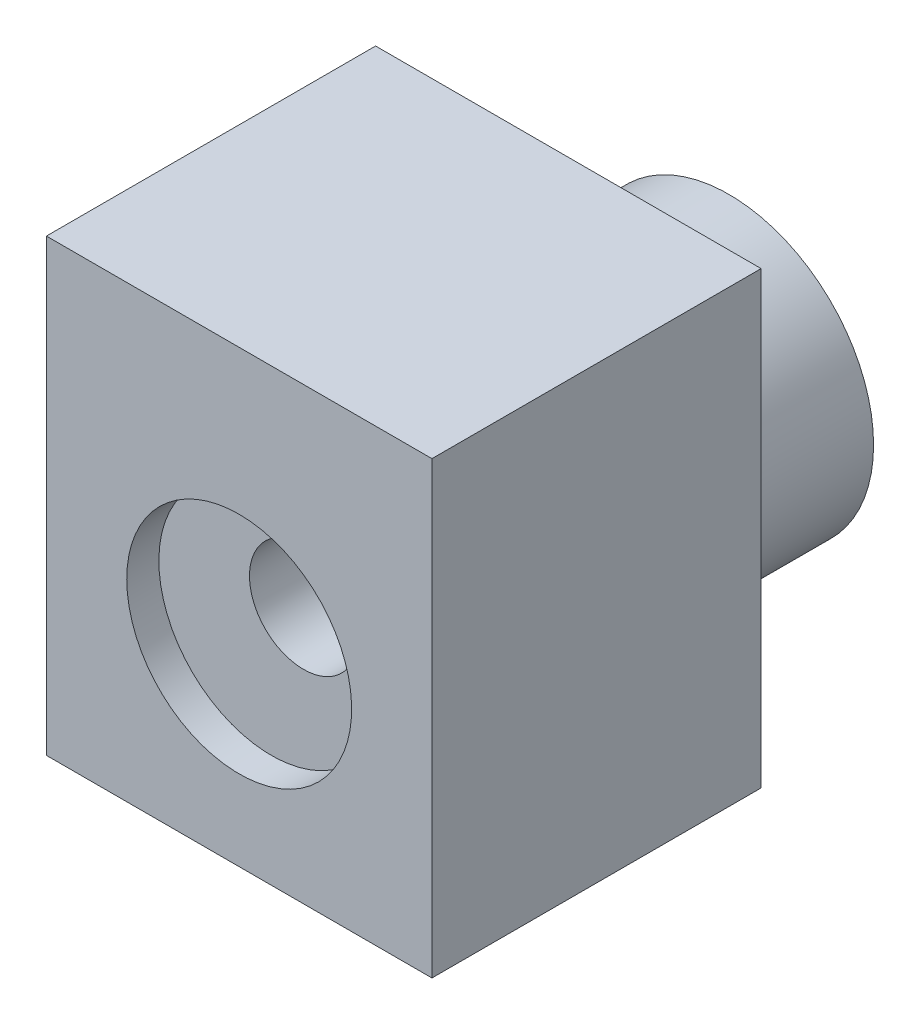
SolidWorks part; units mm, degrees
ref_plane "Płaszczyzna przednia" through (0, 0, 0) normal (0, 0, 1) x (1, 0, 0)
ref_plane "Płaszczyzna górna" through (0, 0, 0) normal (0, 1, 0) x (1, 0, 0)
ref_plane "Płaszczyzna prawa" through (0, 0, 0) normal (1, 0, 0) x (0, 0, -1)
sketch "Szkic2" plane through (0, 0, 0) normal (0, 1, 0) x (1, 0, 0)
  line L0 (13.5, 19) -> (9.3722, 19) construction
  line L1 (-30, 14) -> (30, 14)
  line L2 (-30, 14) -> (-30, 65.2287)
  line L3 (-30, 65.2287) -> (30, 65.2287)
  line L4 (30, 14) -> (30, 65.2287)
  line L5 (-30, 14) -> (30, 65.2287) construction
  line L6 (-30, 65.2287) -> (30, 14) construction
  line L7 (-12, 60.2287) -> (12, 60.2287) construction
  line L8 (0, 0) -> (0, 144.3077) construction
  point P0 (0, 39.6144)
  point P12 (0, 0)
  dimension "D1" = 5
  dimension "D2" = 5
  dimension "D3" = 60
extrude "Dodanie-wyciągnięcie1" add sketch "Szkic2" against normal blind 30 and the other way blind 40
sketch "Szkic3" plane through (0, 0, -14) normal (0, 0, 1) x (1, 0, 0)
  circle A0 centre (0, 0) radius 8 construction
  circle A1 centre (0, 0) radius 8 construction
  circle A2 centre (0, 0) radius 8.4
  dimension "D1" = 0.4
extrude "Wytnij-wyciągnięcie1" cut sketch "Szkic3" against normal through all
ref_plane "Płaszczyzna1" through (0, 0, -39.6144) normal (0, 0, -1) x (-1, 0, 0)
sketch "Szkic5" plane through (0, 0, -65.2287) normal (0, 0, -1) x (-1, 0, 0)
  circle A0 centre (0, 0) radius 17.5
  dimension "D1" = 35
extrude "Wytnij-wyciągnięcie2" cut sketch "Szkic5" against normal blind 10
sketch "Szkic6" plane through (-30, 0, 0) normal (-1, 0, 0) x (0, 0, 1)
  line L0 (-60.2287, -12) -> (-60.2287, 12) construction
  line L1 (-60.2287, -12) -> (-60.2287, 12) construction
  line L2 (0, 0) -> (-81.559, 0) construction
  line L4 (-60.2287, -26.5) -> (-55.2287, -26.5)
  line L5 (-60.2287, -26.5) -> (-60.2287, 26.5)
  line L6 (-60.2287, 26.5) -> (-55.2287, 26.5)
  line L7 (-55.2287, -26.5) -> (-55.2287, 26.5)
  point P9 (-60.2287, 0)
  dimension "D1" = 5
  dimension "D2" = 53
extrude "Wytnij-wyciągnięcie3" cut sketch "Szkic6" against normal offset from surface (55 mm away) 25 up to plane "Płaszczyzna prawa" offset beyond the face yes
mirror "Lustro1" about plane through (0, 0, -39.6144) normal (0, 0, -1) of "Wytnij-wyciągnięcie3", "Wytnij-wyciągnięcie2"
sketch "Szkic8" plane through (0, 0, -65.2287) normal (0, 0, -1) x (-1, 0, 0)
  circle A0 centre (0, 0) radius 17.5 construction
  circle A1 centre (0, 0) radius 17.5
  circle A2 centre (0, 0) radius 22.5
  dimension "D1" = 5
extrude "Dodanie-wyciągnięcie3" add sketch "Szkic8" along normal blind 25
